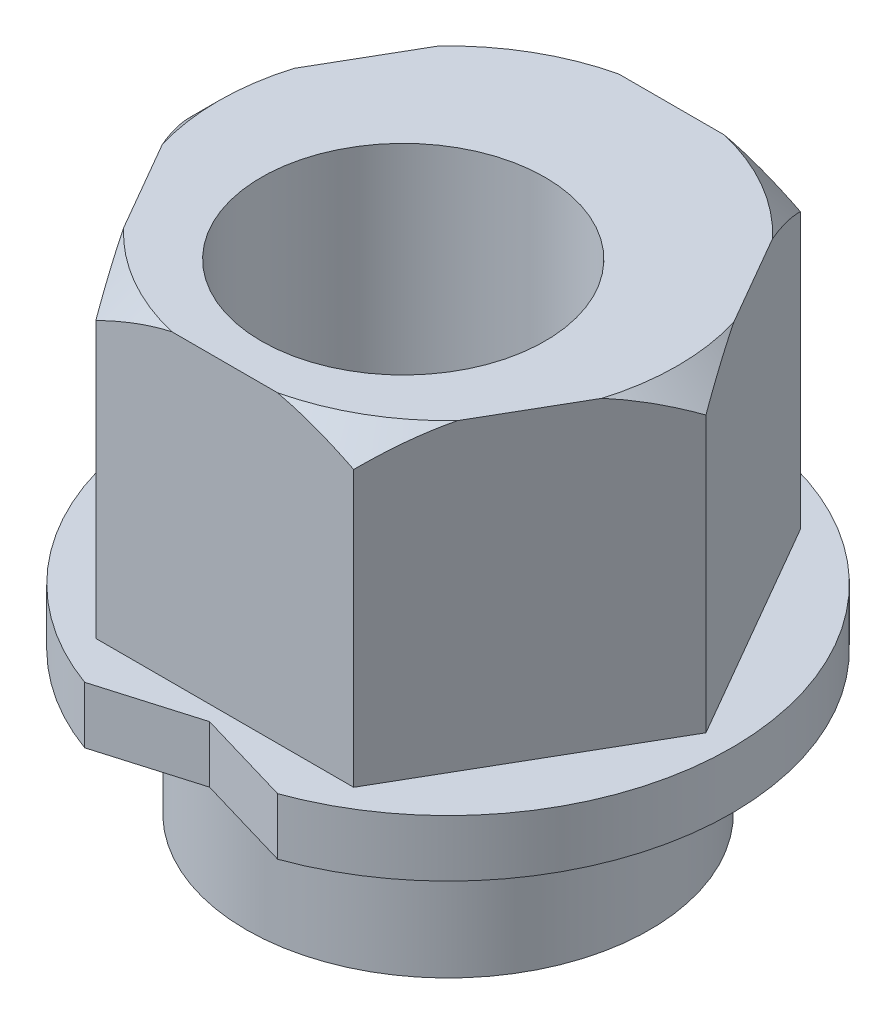
SolidWorks part; units mm, degrees
material "AISI 304"
ref_plane "Front Plane" through (0, 0, 0) normal (0, 0, 1) x (1, 0, 0)
ref_plane "Top Plane" through (0, 0, 0) normal (0, 1, 0) x (1, 0, 0)
ref_plane "Right Plane" through (0, 0, 0) normal (1, 0, 0) x (0, 0, -1)
sketch "Sketch1" plane through (0, 0, 0) normal (0, 1, 0) x (1, 0, 0)
  line L1 (4.5437, 0) -> (2.2719, 3.935)
  line L2 (2.2719, 3.935) -> (-2.2719, 3.935)
  line L3 (-2.2719, 3.935) -> (-4.5437, 0)
  line L4 (-4.5437, 0) -> (-2.2719, -3.935)
  line L5 (-2.2719, -3.935) -> (2.2719, -3.935)
  line L6 (2.2719, -3.935) -> (4.5437, 0)
  circle A0 centre (0, 0) radius 3.935 construction
  dimension "D1" = 7.87
extrude "Boss-Extrude1" add sketch "Sketch1" along normal blind 5.35
sketch "Sketch2" plane through (0, 0, 0) normal (0, 1, 0) x (1, 0, 0)
  circle A0 centre (0, 0) radius 5
  dimension "D1" = 10
extrude "Boss-Extrude2" add sketch "Sketch2" against normal blind 1
sketch "Sketch3" plane through (0, -1, 0) normal (0, -1, 0) x (1, 0, 0)
  circle A0 centre (0, 0) radius 3.555
  dimension "D1" = 7.11
extrude "Boss-Extrude3" add sketch "Sketch3" along normal blind 2.5
sketch "Sketch4" plane through (0, 5.35, 0) normal (0, 1, 0) x (1, 0, 0)
  line L0 (0, 0) -> (0, -0.79) construction
  circle A0 centre (0, -0.79) radius 2.5
  dimension "D1" = 5
  dimension "D2" = 0.79
extrude "Cut-Extrude1" cut sketch "Sketch4" against normal through all
sketch "Sketch5" plane through (0, 0, 0) normal (0, 1, 0) x (1, 0, 0)
  line L0 (-1.7, -4.7021) -> (0, -4.2021)
  line L1 (0, -4.2021) -> (1.7, -4.7021)
  circle A0 centre (0, 0) radius 5 construction
  arc A1 (-1.7, -4.7021) -> (1.7, -4.7021) centre (0, 0) ccw
  dimension "D1" = 3.4
  dimension "D2" = 0.5
extrude "Cut-Extrude2" cut sketch "Sketch5" against normal through all
sketch "Sketch6" plane through (0, 0, 0) normal (0, 0, 1) x (1, 0, 0)
  line L0 (0, 0) -> (0, 6.4706) construction
  line L1 (4.0437, 5.35) -> (4.5437, 5.35)
  line L2 (2.2719, 5.35) -> (4.5437, 5.35) construction
  line L3 (4.5437, 5.35) -> (4.5437, 4.85)
  line L4 (4.5437, 5.35) -> (4.5437, 0) construction
  line L5 (4.5437, 4.85) -> (4.0437, 5.35)
  dimension "D1" = 0.5
revolve "Cut-Revolve1" cut sketch "Sketch6" angle 360 about L0
